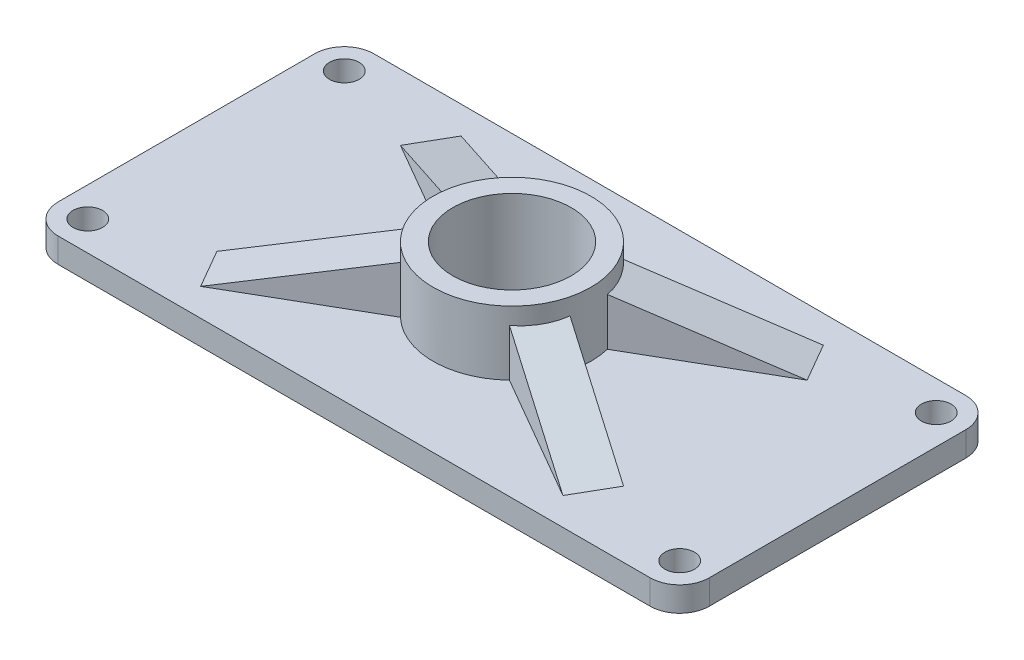
SolidWorks part; units mm, degrees
material "Thornel Mat VMA"
ref_plane "Front Plane" through (0, 0, 0) normal (0, 0, 1) x (1, 0, 0)
ref_plane "Top Plane" through (0, 0, 0) normal (0, 1, 0) x (1, 0, 0)
ref_plane "Right Plane" through (0, 0, 0) normal (1, 0, 0) x (0, 0, -1)
sketch "Sketch1" plane through (0, 0, 0) normal (0, 1, 0) x (1, 0, 0)
  line L1 (-60, -32) -> (60, -32)
  line L2 (-66, -26) -> (-66, 26)
  line L3 (-60, 32) -> (60, 32)
  line L4 (66, -26) -> (66, 26)
  line L5 (-66, -32) -> (66, 32) construction
  line L6 (-66, 32) -> (66, -32) construction
  circle A0 centre (0, 0) radius 12
  circle A1 centre (60, 26) radius 3
  circle A2 centre (60, -26) radius 3
  circle A3 centre (-60, -26) radius 3
  circle A4 centre (-60, 26) radius 3
  arc A6 (-60, -32) -> (-66, -26) centre (-60, -26) cw
  arc A7 (60, -32) -> (66, -26) centre (60, -26) ccw
  arc A8 (60, 32) -> (66, 26) centre (60, 26) cw
  arc A9 (-66, 26) -> (-60, 32) centre (-60, 26) cw
  point P0 (0, 0)
  point P14 (0, 0)
  point P19 (0, 0)
  point P25 (0, 0)
  point P29 (0, 0)
  point P30 (0, 0)
  dimension "D3" = 24
  dimension "D5" = 6
  dimension "D6" = 6
  dimension "D1" = 132
  dimension "D2" = 64
extrude "Boss-Extrude2" add sketch "Sketch1" along normal blind 5
sketch "Sketch2" plane through (0, 5, 0) normal (0, 1, 0) x (1, 0, 0)
  circle A0 centre (0, 0) radius 12
  circle A1 centre (0, 0) radius 16
  dimension "D1" = 24
  dimension "D2" = 32
extrude "Boss-Extrude3" add sketch "Sketch2" along normal blind 13
sketch "Sketch3" plane through (0, 5, 0) normal (0, 1, 0) x (1, 0, 0)
  line L0 (0, 0) -> (50000, 0) construction
  line L2 (0, 0) -> (28.726, -16.585) construction
  point P6 (0, 0)
  dimension "D1" = 30
ref_plane "Plane1" through (0, 0, 0) normal (-0.5, 0, 0.866) x (0.866, 0, 0.5)
sketch "Sketch4" plane through (0, 0, 0) normal (-0.5, 0, 0.866) x (0.866, 0, 0.5)
  line L10 (-12, 15.7223) -> (-45, 5)
  line L11 (-173205.0808, 5) -> (216506.3509, 5) construction
  line L12 (-45, 5) -> (-12, 5)
  line L13 (-12, 5) -> (-12, 15.7223)
  line L14 (12, 15.7223) -> (12, 5)
  line L15 (12, 5) -> (45, 5)
  line L16 (45, 5) -> (12, 15.7223)
  dimension "D1" = 12
  dimension "D2" = 12
  dimension "D3" = 45
  dimension "D4" = 45
  dimension "D5" = 162
  dimension "D6" = 162
extrude "Boss-Extrude9" add sketch "Sketch4" along normal mid plane 9
mirror "Mirror1" about plane through (0, 0, 0) normal (0, 0, 1) of "Boss-Extrude9"
